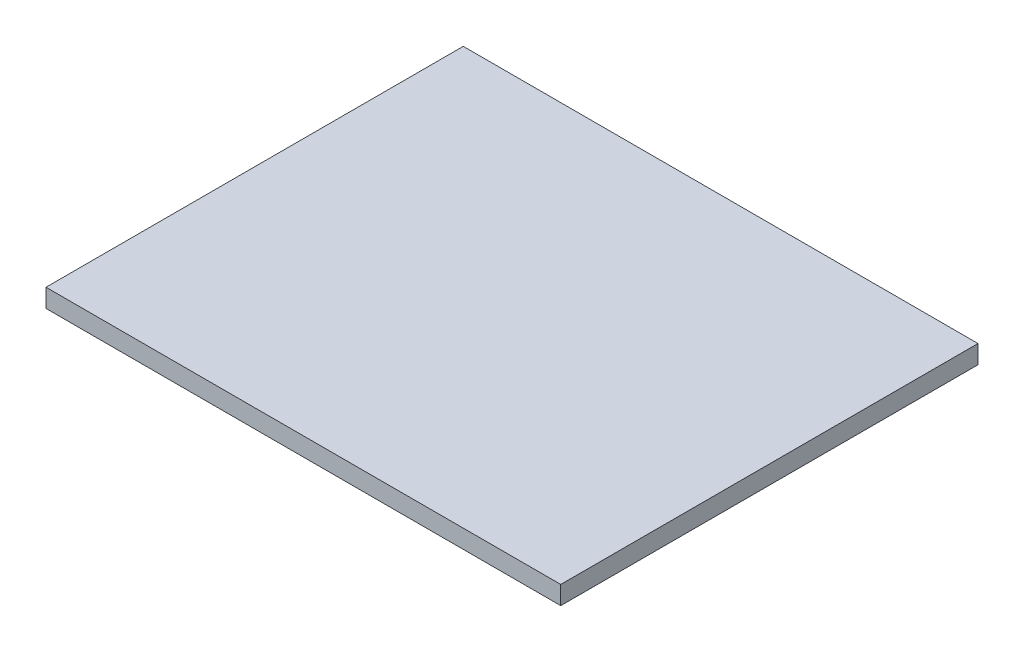
SolidWorks part; units mm, degrees
ref_plane "Front Plane" through (0, 0, 0) normal (0, 0, 1) x (1, 0, 0)
ref_plane "Top Plane" through (0, 0, 0) normal (0, 1, 0) x (1, 0, 0)
ref_plane "Right Plane" through (0, 0, 0) normal (1, 0, 0) x (0, 0, -1)
sketch "Sketch1" plane through (0, 0, 0) normal (0, 1, 0) x (1, 0, 0)
  line L1 (0, 0) -> (83.9192, 0)
  line L2 (0, 0) -> (0, 68.0248)
  line L3 (0, 68.0248) -> (83.9192, 68.0248)
  line L4 (83.9192, 0) -> (83.9192, 68.0248)
  line L5 (0, 0) -> (83.9192, 68.0248) construction
  line L6 (0, 68.0248) -> (83.9192, 0) construction
  point P4 (41.9596, 34.0124)
extrude "Boss-Extrude1" add sketch "Sketch1" along normal blind 3
